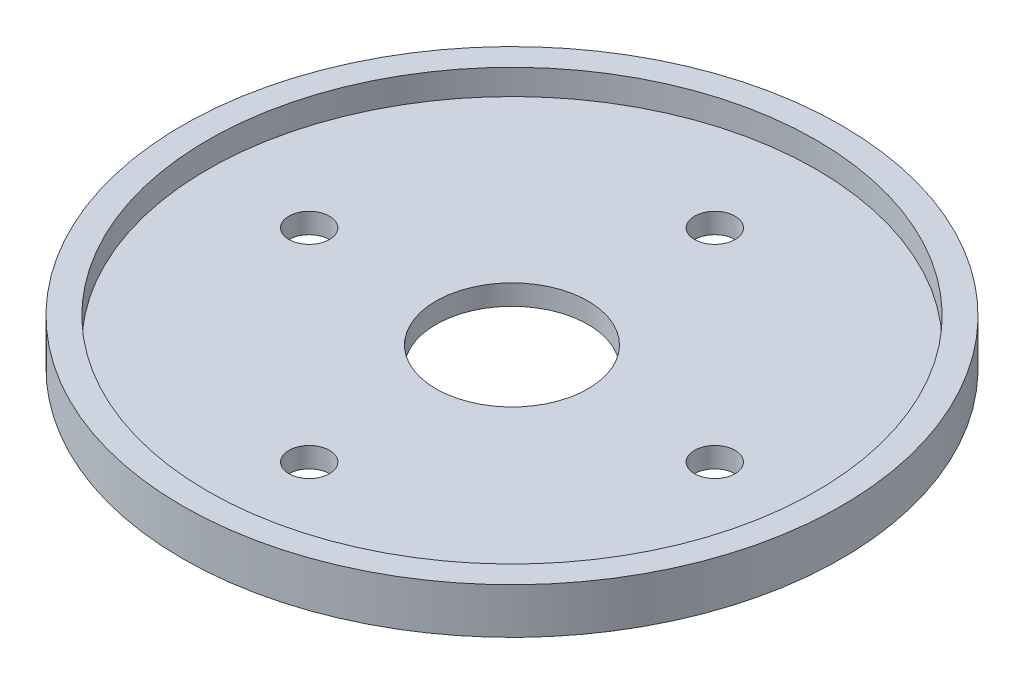
SolidWorks part; units mm, degrees
material "1060 Alloy"
ref_plane "Front Plane" through (0, 0, 0) normal (0, 0, 1) x (1, 0, 0)
ref_plane "Top Plane" through (0, 0, 0) normal (0, 1, 0) x (1, 0, 0)
ref_plane "Right Plane" through (0, 0, 0) normal (1, 0, 0) x (0, 0, -1)
sketch "Sketch1" plane through (0, 0, 0) normal (0, 1, 0) x (1, 0, 0)
  line L0 (0, 25.4) -> (0, -25.4) construction
  line L2 (-25.4, 0) -> (25.4, 0) construction
  circle A0 centre (0, 0) radius 41.275
  circle A1 centre (0, 0) radius 38.1
  circle A2 centre (0, 0) radius 9.525
  circle A3 centre (0, 25.4) radius 2.54
  circle A4 centre (25.4, 0) radius 2.54
  circle A5 centre (0, -25.4) radius 2.54
  circle A6 centre (-25.4, 0) radius 2.54
  circle A7 centre (0, 0) radius 25.4 construction
  dimension "D1" = 82.55
  dimension "D2" = 76.2
  dimension "D3" = 50.8
  dimension "D4" = 19.05
  dimension "D5" = 5.08
extrude "base" add sketch "Sketch1" along normal blind 2.54 contours A1 A6 A5 A4 A3 A2 | A0 A1
sketch "Sketch2" plane through (0, 2.54, 0) normal (0, 1, 0) x (1, 0, 0)
  circle A0 centre (0, 0) radius 38.1
  circle A2 centre (0, 0) radius 41.275
  circle A3 centre (0, 0) radius 41.275
  dimension "D1" = 76.2
  dimension "D2" = 0
extrude "front wall" add sketch "Sketch2" along normal blind 3.175
